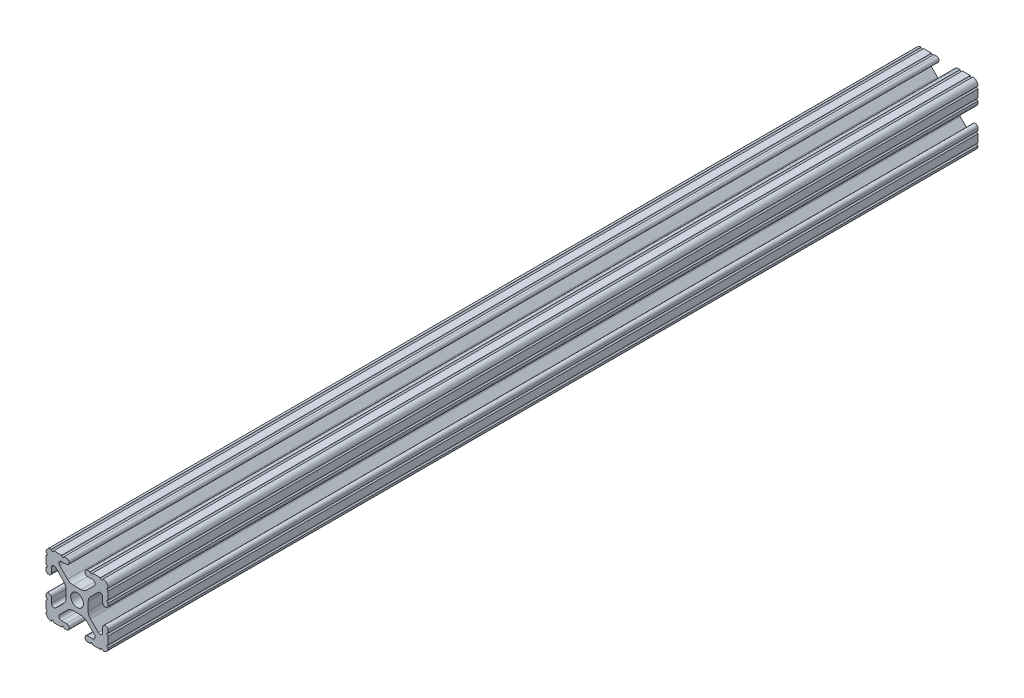
SolidWorks part; units mm, degrees
ref_plane "Front Plane" through (0, 0, 0) normal (0, 0, 1) x (1, 0, 0)
ref_plane "Top Plane" through (0, 0, 0) normal (0, 1, 0) x (1, 0, 0)
ref_plane "Right Plane" through (0, 0, 0) normal (1, 0, 0) x (0, 0, -1)
sketch "Sketch1" plane through (0, 0, 0) normal (1, 0, 0) x (0, 0, -1)
  line L0 (0, 0) -> (-355.6, 0)
  dimension "D1" = 355.6
other "Fractional 1010(1)"
ref_plane "Plane1" through (0, 0, 0) normal (0, 0, 1) x (0, -1, 0)
sketch "Sketch11" plane through (0, 0, 0) normal (0, 0, 1) x (0, -1, 0)
  line L0 (10.5918, 12.7) -> (10.5664, 12.7)
  line L1 (9.5504, 12.7) -> (6.3246, 12.7)
  line L2 (5.3086, 12.7) -> (4.3561, 12.7)
  line L3 (4.3561, 10.4902) -> (6.3701, 10.4902)
  line L4 (7.1192, 8.6817) -> (3.8846, 5.4471)
  line L5 (1.6396, 4.5172) -> (-1.6396, 4.5172)
  line L6 (-3.8846, 5.4471) -> (-7.1192, 8.6817)
  line L7 (-6.3701, 10.4902) -> (-4.3561, 10.4902)
  line L8 (-4.3561, 12.7) -> (-5.3086, 12.7)
  line L9 (-6.3246, 12.7) -> (-9.5504, 12.7)
  line L10 (-10.5664, 12.7) -> (-10.5918, 12.7)
  line L11 (-12.7, 10.5918) -> (-12.7, 10.5664)
  line L12 (-12.7, 9.5504) -> (-12.7, 6.3246)
  line L13 (-12.7, 5.3086) -> (-12.7, 4.3561)
  line L14 (-10.4902, 4.3561) -> (-10.4902, 6.3701)
  line L15 (-8.6817, 7.1192) -> (-5.4471, 3.8846)
  line L16 (-4.5172, 1.6396) -> (-4.5172, -1.6396)
  line L17 (-5.4471, -3.8846) -> (-8.6817, -7.1192)
  line L18 (-10.4902, -6.3701) -> (-10.4902, -4.3561)
  line L19 (-12.7, -4.3561) -> (-12.7, -5.3086)
  line L20 (-12.7, -6.3246) -> (-12.7, -9.5504)
  line L21 (-12.7, -10.5664) -> (-12.7, -10.5918)
  line L22 (-10.5918, -12.7) -> (-10.5664, -12.7)
  line L23 (-9.5504, -12.7) -> (-6.3246, -12.7)
  line L24 (-5.3086, -12.7) -> (-4.3561, -12.7)
  line L25 (-4.3561, -10.4902) -> (-6.3701, -10.4902)
  line L26 (-7.1192, -8.6817) -> (-3.8846, -5.4471)
  line L27 (-1.6396, -4.5172) -> (1.6396, -4.5172)
  line L28 (3.8846, -5.4471) -> (7.1192, -8.6817)
  line L29 (6.3701, -10.4902) -> (4.3561, -10.4902)
  line L30 (4.3561, -12.7) -> (5.3086, -12.7)
  line L31 (6.3246, -12.7) -> (9.5504, -12.7)
  line L32 (10.5664, -12.7) -> (10.5918, -12.7)
  line L33 (12.7, -10.5918) -> (12.7, -10.5664)
  line L34 (12.7, -9.5504) -> (12.7, -6.3246)
  line L35 (12.7, -5.3086) -> (12.7, -4.3561)
  line L36 (10.4902, -4.3561) -> (10.4902, -6.3701)
  line L37 (8.6817, -7.1192) -> (5.4471, -3.8846)
  line L38 (4.5172, -1.6396) -> (4.5172, 1.6396)
  line L39 (5.4471, 3.8846) -> (8.6817, 7.1192)
  line L40 (10.4902, 6.3701) -> (10.4902, 4.3561)
  line L41 (12.7, 4.3561) -> (12.7, 5.3086)
  line L42 (12.7, 6.3246) -> (12.7, 9.5504)
  line L43 (12.7, 10.5664) -> (12.7, 10.5918)
  circle A0 centre (0, 0) radius 2.6035
  arc A1 (12.7, 10.5918) -> (10.5918, 12.7) centre (10.5918, 10.5918) ccw
  arc A2 (9.5504, 12.7) -> (10.5664, 12.7) centre (10.0584, 12.7) ccw
  arc A3 (5.3086, 12.7) -> (6.3246, 12.7) centre (5.8166, 12.7) ccw
  arc A4 (4.3561, 12.7) -> (4.3561, 10.4902) centre (4.3561, 11.5951) ccw
  arc A5 (7.1192, 8.6817) -> (6.3701, 10.4902) centre (6.3701, 9.4308) ccw
  arc A6 (1.6396, 4.5172) -> (3.8846, 5.4471) centre (1.6396, 7.6922) ccw
  arc A7 (-3.8846, 5.4471) -> (-1.6396, 4.5172) centre (-1.6396, 7.6922) ccw
  arc A8 (-6.3701, 10.4902) -> (-7.1192, 8.6817) centre (-6.3701, 9.4308) ccw
  arc A9 (-4.3561, 10.4902) -> (-4.3561, 12.7) centre (-4.3561, 11.5951) ccw
  arc A10 (-6.3246, 12.7) -> (-5.3086, 12.7) centre (-5.8166, 12.7) ccw
  arc A11 (-10.5664, 12.7) -> (-9.5504, 12.7) centre (-10.0584, 12.7) ccw
  arc A12 (-10.5918, 12.7) -> (-12.7, 10.5918) centre (-10.5918, 10.5918) ccw
  arc A13 (-12.7, 9.5504) -> (-12.7, 10.5664) centre (-12.7, 10.0584) ccw
  arc A14 (-12.7, 5.3086) -> (-12.7, 6.3246) centre (-12.7, 5.8166) ccw
  arc A15 (-12.7, 4.3561) -> (-10.4902, 4.3561) centre (-11.5951, 4.3561) ccw
  arc A16 (-8.6817, 7.1192) -> (-10.4902, 6.3701) centre (-9.4308, 6.3701) ccw
  arc A17 (-4.5172, 1.6396) -> (-5.4471, 3.8846) centre (-7.6922, 1.6396) ccw
  arc A18 (-5.4471, -3.8846) -> (-4.5172, -1.6396) centre (-7.6922, -1.6396) ccw
  arc A19 (-10.4902, -6.3701) -> (-8.6817, -7.1192) centre (-9.4308, -6.3701) ccw
  arc A20 (-10.4902, -4.3561) -> (-12.7, -4.3561) centre (-11.5951, -4.3561) ccw
  arc A21 (-12.7, -6.3246) -> (-12.7, -5.3086) centre (-12.7, -5.8166) ccw
  arc A22 (-12.7, -10.5664) -> (-12.7, -9.5504) centre (-12.7, -10.0584) ccw
  arc A23 (-12.7, -10.5918) -> (-10.5918, -12.7) centre (-10.5918, -10.5918) ccw
  arc A24 (-9.5504, -12.7) -> (-10.5664, -12.7) centre (-10.0584, -12.7) ccw
  arc A25 (-5.3086, -12.7) -> (-6.3246, -12.7) centre (-5.8166, -12.7) ccw
  arc A26 (-4.3561, -12.7) -> (-4.3561, -10.4902) centre (-4.3561, -11.5951) ccw
  arc A27 (-7.1192, -8.6817) -> (-6.3701, -10.4902) centre (-6.3701, -9.4308) ccw
  arc A28 (-1.6396, -4.5172) -> (-3.8846, -5.4471) centre (-1.6396, -7.6922) ccw
  arc A29 (3.8846, -5.4471) -> (1.6396, -4.5172) centre (1.6396, -7.6922) ccw
  arc A30 (6.3701, -10.4902) -> (7.1192, -8.6817) centre (6.3701, -9.4308) ccw
  arc A31 (4.3561, -10.4902) -> (4.3561, -12.7) centre (4.3561, -11.5951) ccw
  arc A32 (6.3246, -12.7) -> (5.3086, -12.7) centre (5.8166, -12.7) ccw
  arc A33 (10.5664, -12.7) -> (9.5504, -12.7) centre (10.0584, -12.7) ccw
  arc A34 (10.5918, -12.7) -> (12.7, -10.5918) centre (10.5918, -10.5918) ccw
  arc A35 (12.7, -9.5504) -> (12.7, -10.5664) centre (12.7, -10.0584) ccw
  arc A36 (12.7, -5.3086) -> (12.7, -6.3246) centre (12.7, -5.8166) ccw
  arc A37 (12.7, -4.3561) -> (10.4902, -4.3561) centre (11.5951, -4.3561) ccw
  arc A38 (8.6817, -7.1192) -> (10.4902, -6.3701) centre (9.4308, -6.3701) ccw
  arc A39 (4.5172, -1.6396) -> (5.4471, -3.8846) centre (7.6922, -1.6396) ccw
  arc A40 (5.4471, 3.8846) -> (4.5172, 1.6396) centre (7.6922, 1.6396) ccw
  arc A41 (10.4902, 6.3701) -> (8.6817, 7.1192) centre (9.4308, 6.3701) ccw
  arc A42 (10.4902, 4.3561) -> (12.7, 4.3561) centre (11.5951, 4.3561) ccw
  arc A43 (12.7, 6.3246) -> (12.7, 5.3086) centre (12.7, 5.8166) ccw
  arc A44 (12.7, 10.5664) -> (12.7, 9.5504) centre (12.7, 10.0584) ccw
  point P0 (0, 0)
